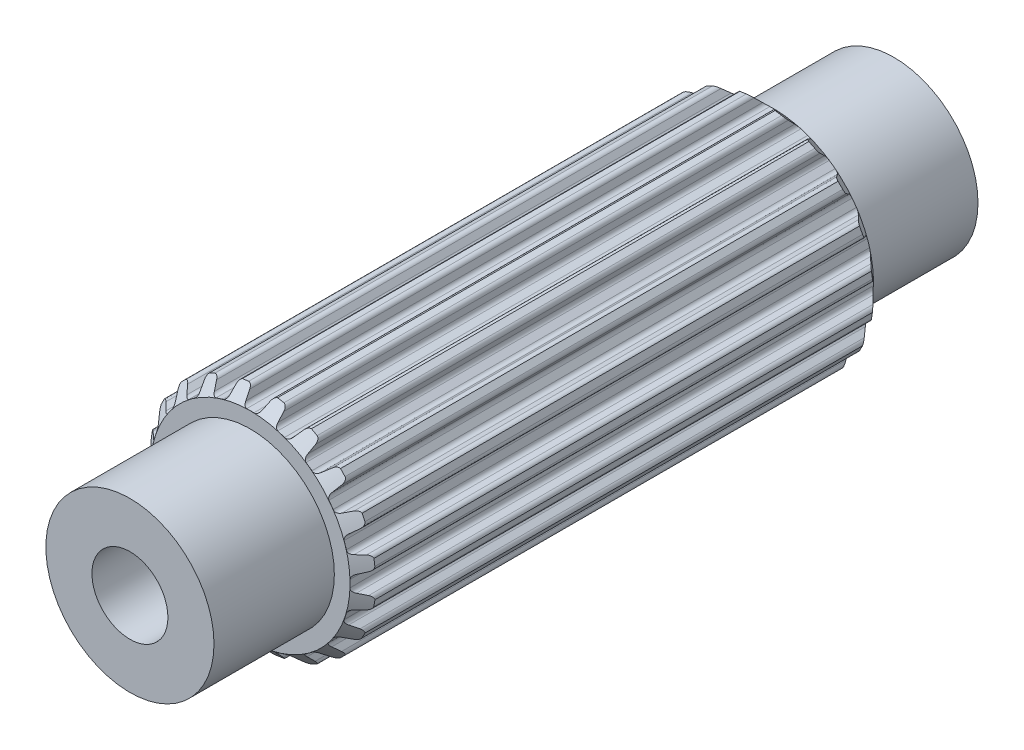
SolidWorks part; units mm, degrees
ref_plane "Front Plane" through (0, 0, 0) normal (0, 0, 1) x (1, 0, 0)
ref_plane "Top Plane" through (0, 0, 0) normal (0, 1, 0) x (1, 0, 0)
ref_plane "Right Plane" through (0, 0, 0) normal (1, 0, 0) x (0, 0, -1)
sketch "Sketch1" plane through (0, 0, 0) normal (0, 0, 1) x (1, 0, 0)
  line L0 (-0.1069, 2.9699) -> (0.1069, 2.9699)
  line L1 (0.3159, 3.2375) -> (0.2537, 3.0575)
  line L2 (-0.2964, 3.2367) -> (-0.2318, 3.0575)
  line L3 (-0.2964, 3.2367) -> (0.3159, 3.2375) construction
  line L4 (0, 3.3252) -> (0, 0) construction
  line L5 (-0.2318, 3.0575) -> (0.2537, 3.0575) construction
  line L6 (-0.4281, 3.3241) -> (0.4281, 3.3263) construction
  line L7 (0.7183, 3.1698) -> (0.7244, 2.9795)
  line L8 (0.816, 2.8576) -> (1.0195, 2.7915)
  line L9 (1.3009, 2.9815) -> (1.1862, 2.8295)
  line L10 (1.6627, 2.7927) -> (1.6097, 2.6099)
  line L11 (1.6591, 2.4655) -> (1.8322, 2.3398)
  line L12 (2.1585, 2.4335) -> (2.0025, 2.3245)
  line L13 (2.4443, 2.1423) -> (2.3374, 1.9847)
  line L14 (2.3398, 1.8322) -> (2.4655, 1.6591)
  line L15 (2.8049, 1.6474) -> (2.6228, 1.5919)
  line L16 (2.9866, 1.2821) -> (2.8363, 1.1653)
  line L17 (2.7915, 1.0195) -> (2.8576, 0.816)
  line L18 (3.1767, 0.7) -> (2.9863, 0.7035)
  line L19 (3.2367, 0.2964) -> (3.0575, 0.2318)
  line L20 (2.9699, 0.1069) -> (2.9699, -0.1069)
  line L21 (3.2375, -0.3159) -> (3.0575, -0.2537)
  line L22 (3.1698, -0.7183) -> (2.9795, -0.7244)
  line L23 (2.8576, -0.816) -> (2.7915, -1.0195)
  line L24 (2.9815, -1.3009) -> (2.8295, -1.1862)
  line L25 (2.7927, -1.6627) -> (2.6099, -1.6097)
  line L26 (2.4655, -1.6591) -> (2.3398, -1.8322)
  line L27 (2.4335, -2.1585) -> (2.3245, -2.0025)
  line L28 (2.1423, -2.4443) -> (1.9847, -2.3374)
  line L29 (1.8322, -2.3398) -> (1.6591, -2.4655)
  line L30 (1.6474, -2.8049) -> (1.5919, -2.6228)
  line L31 (1.2821, -2.9866) -> (1.1653, -2.8363)
  line L32 (1.0195, -2.7915) -> (0.816, -2.8576)
  line L33 (0.7, -3.1767) -> (0.7035, -2.9863)
  line L34 (0.2964, -3.2367) -> (0.2318, -3.0575)
  line L35 (0.1069, -2.9699) -> (-0.1069, -2.9699)
  line L36 (-0.3159, -3.2375) -> (-0.2537, -3.0575)
  line L37 (-0.7183, -3.1698) -> (-0.7244, -2.9795)
  line L38 (-0.816, -2.8576) -> (-1.0195, -2.7915)
  line L39 (-1.3009, -2.9815) -> (-1.1862, -2.8295)
  line L40 (-1.6627, -2.7927) -> (-1.6097, -2.6099)
  line L41 (-1.6591, -2.4655) -> (-1.8322, -2.3398)
  line L42 (-2.1585, -2.4335) -> (-2.0025, -2.3245)
  line L43 (-2.4443, -2.1423) -> (-2.3374, -1.9847)
  line L44 (-2.3398, -1.8322) -> (-2.4655, -1.6591)
  line L45 (-2.8049, -1.6474) -> (-2.6228, -1.5919)
  line L46 (-2.9866, -1.2821) -> (-2.8363, -1.1653)
  line L47 (-2.7915, -1.0195) -> (-2.8576, -0.816)
  line L48 (-3.1767, -0.7) -> (-2.9863, -0.7035)
  line L49 (-3.2367, -0.2964) -> (-3.0575, -0.2318)
  line L50 (-2.9699, -0.1069) -> (-2.9699, 0.1069)
  line L51 (-3.2375, 0.3159) -> (-3.0575, 0.2537)
  line L52 (-3.1698, 0.7183) -> (-2.9795, 0.7244)
  line L53 (-2.8576, 0.816) -> (-2.7915, 1.0195)
  line L54 (-2.9815, 1.3009) -> (-2.8295, 1.1862)
  line L55 (-2.7927, 1.6627) -> (-2.6099, 1.6097)
  line L56 (-2.4655, 1.6591) -> (-2.3398, 1.8322)
  line L57 (-2.4335, 2.1585) -> (-2.3245, 2.0025)
  line L58 (-2.1423, 2.4443) -> (-1.9847, 2.3374)
  line L59 (-1.8322, 2.3398) -> (-1.6591, 2.4655)
  line L60 (-1.6474, 2.8049) -> (-1.5919, 2.6228)
  line L61 (-1.2821, 2.9866) -> (-1.1653, 2.8363)
  line L62 (-1.0195, 2.7915) -> (-0.816, 2.8576)
  line L63 (-0.7, 3.1767) -> (-0.7035, 2.9863)
  line L64 (0.4281, 3.3263) -> (0.62, 3.2938)
  line L65 (1.4351, 3.0312) -> (1.6075, 2.9409)
  line L66 (2.3015, 2.4394) -> (2.4376, 2.3003)
  line L67 (2.9427, 1.6088) -> (3.0291, 1.4344)
  line L68 (3.2958, 0.6207) -> (3.3241, 0.4281)
  line L69 (3.3263, -0.4281) -> (3.2938, -0.62)
  line L70 (3.0312, -1.4351) -> (2.9409, -1.6075)
  line L71 (2.4394, -2.3015) -> (2.3003, -2.4376)
  line L72 (1.6088, -2.9427) -> (1.4344, -3.0291)
  line L73 (0.6207, -3.2958) -> (0.4281, -3.3241)
  line L74 (-0.4281, -3.3263) -> (-0.62, -3.2938)
  line L75 (-1.4351, -3.0312) -> (-1.6075, -2.9409)
  line L76 (-2.3015, -2.4394) -> (-2.4376, -2.3003)
  line L77 (-2.9427, -1.6088) -> (-3.0291, -1.4344)
  line L78 (-3.2958, -0.6207) -> (-3.3241, -0.4281)
  line L79 (-3.3263, 0.4281) -> (-3.2938, 0.62)
  line L80 (-3.0312, 1.4351) -> (-2.9409, 1.6075)
  line L81 (-2.4394, 2.3015) -> (-2.3003, 2.4376)
  line L82 (-1.6088, 2.9427) -> (-1.4344, 3.0291)
  line L83 (-0.6207, 3.2958) -> (-0.4281, 3.3241)
  arc A0 (0.2537, 3.0575) -> (0.1069, 2.9699) centre (0.1283, 3.1009) cw
  arc A1 (-0.2318, 3.0575) -> (-0.1069, 2.9699) centre (-0.1069, 3.1026) ccw
  arc A2 (0.62, 3.2938) -> (0.7183, 3.1698) centre (0.5856, 3.1656) cw
  arc A3 (0.7244, 2.9795) -> (0.816, 2.8576) centre (0.857, 2.9838) ccw
  arc A4 (-0.4281, 3.3241) -> (-0.2964, 3.2367) centre (-0.4213, 3.1916) cw
  arc A5 (0.4281, 3.3263) -> (0.3159, 3.2375) centre (0.4413, 3.1942) ccw
  arc A6 (1.1862, 2.8295) -> (1.0195, 2.7915) centre (1.0802, 2.9095) cw
  arc A7 (1.4351, 3.0312) -> (1.3009, 2.9815) centre (1.4068, 2.9015) ccw
  arc A8 (1.6075, 2.9409) -> (1.6627, 2.7927) centre (1.5352, 2.8297) cw
  arc A9 (1.6097, 2.6099) -> (1.6591, 2.4655) centre (1.7371, 2.5729) ccw
  arc A10 (2.0025, 2.3245) -> (1.8322, 2.3398) centre (1.9264, 2.4332) cw
  arc A11 (2.3015, 2.4394) -> (2.1585, 2.4335) centre (2.2346, 2.3248) ccw
  arc A12 (2.4376, 2.3003) -> (2.4443, 2.1423) centre (2.3345, 2.2168) cw
  arc A13 (2.3374, 1.9847) -> (2.3398, 1.8322) centre (2.4472, 1.9102) ccw
  arc A14 (2.6228, 1.5919) -> (2.4655, 1.6591) centre (2.5841, 1.7189) cw
  arc A15 (2.9427, 1.6088) -> (2.8049, 1.6474) centre (2.8436, 1.5205) ccw
  arc A16 (3.0291, 1.4344) -> (2.9866, 1.2821) centre (2.9052, 1.3869) cw
  arc A17 (2.8363, 1.1653) -> (2.7915, 1.0195) centre (2.9177, 1.0605) ccw
  arc A18 (2.9863, 0.7035) -> (2.8576, 0.816) centre (2.9887, 0.8362) cw
  arc A19 (3.2958, 0.6207) -> (3.1767, 0.7) centre (3.1743, 0.5673) ccw
  arc A20 (3.3241, 0.4281) -> (3.2367, 0.2964) centre (3.1916, 0.4213) cw
  arc A21 (3.0575, 0.2318) -> (2.9699, 0.1069) centre (3.1026, 0.1069) ccw
  arc A22 (3.0575, -0.2537) -> (2.9699, -0.1069) centre (3.1009, -0.1283) cw
  arc A23 (3.3263, -0.4281) -> (3.2375, -0.3159) centre (3.1942, -0.4413) ccw
  arc A24 (3.2938, -0.62) -> (3.1698, -0.7183) centre (3.1656, -0.5856) cw
  arc A25 (2.9795, -0.7244) -> (2.8576, -0.816) centre (2.9838, -0.857) ccw
  arc A26 (2.8295, -1.1862) -> (2.7915, -1.0195) centre (2.9095, -1.0802) cw
  arc A27 (3.0312, -1.4351) -> (2.9815, -1.3009) centre (2.9015, -1.4068) ccw
  arc A28 (2.9409, -1.6075) -> (2.7927, -1.6627) centre (2.8297, -1.5352) cw
  arc A29 (2.6099, -1.6097) -> (2.4655, -1.6591) centre (2.5729, -1.7371) ccw
  arc A30 (2.3245, -2.0025) -> (2.3398, -1.8322) centre (2.4332, -1.9264) cw
  arc A31 (2.4394, -2.3015) -> (2.4335, -2.1585) centre (2.3248, -2.2346) ccw
  arc A32 (2.3003, -2.4376) -> (2.1423, -2.4443) centre (2.2168, -2.3345) cw
  arc A33 (1.9847, -2.3374) -> (1.8322, -2.3398) centre (1.9102, -2.4472) ccw
  arc A34 (1.5919, -2.6228) -> (1.6591, -2.4655) centre (1.7189, -2.5841) cw
  arc A35 (1.6088, -2.9427) -> (1.6474, -2.8049) centre (1.5205, -2.8436) ccw
  arc A36 (1.4344, -3.0291) -> (1.2821, -2.9866) centre (1.3869, -2.9052) cw
  arc A37 (1.1653, -2.8363) -> (1.0195, -2.7915) centre (1.0605, -2.9177) ccw
  arc A38 (0.7035, -2.9863) -> (0.816, -2.8576) centre (0.8362, -2.9887) cw
  arc A39 (0.6207, -3.2958) -> (0.7, -3.1767) centre (0.5673, -3.1743) ccw
  arc A40 (0.4281, -3.3241) -> (0.2964, -3.2367) centre (0.4213, -3.1916) cw
  arc A41 (0.2318, -3.0575) -> (0.1069, -2.9699) centre (0.1069, -3.1026) ccw
  arc A42 (-0.2537, -3.0575) -> (-0.1069, -2.9699) centre (-0.1283, -3.1009) cw
  arc A43 (-0.4281, -3.3263) -> (-0.3159, -3.2375) centre (-0.4413, -3.1942) ccw
  arc A44 (-0.62, -3.2938) -> (-0.7183, -3.1698) centre (-0.5856, -3.1656) cw
  arc A45 (-0.7244, -2.9795) -> (-0.816, -2.8576) centre (-0.857, -2.9838) ccw
  arc A46 (-1.1862, -2.8295) -> (-1.0195, -2.7915) centre (-1.0802, -2.9095) cw
  arc A47 (-1.4351, -3.0312) -> (-1.3009, -2.9815) centre (-1.4068, -2.9015) ccw
  arc A48 (-1.6075, -2.9409) -> (-1.6627, -2.7927) centre (-1.5352, -2.8297) cw
  arc A49 (-1.6097, -2.6099) -> (-1.6591, -2.4655) centre (-1.7371, -2.5729) ccw
  arc A50 (-2.0025, -2.3245) -> (-1.8322, -2.3398) centre (-1.9264, -2.4332) cw
  arc A51 (-2.3015, -2.4394) -> (-2.1585, -2.4335) centre (-2.2346, -2.3248) ccw
  arc A52 (-2.4376, -2.3003) -> (-2.4443, -2.1423) centre (-2.3345, -2.2168) cw
  arc A53 (-2.3374, -1.9847) -> (-2.3398, -1.8322) centre (-2.4472, -1.9102) ccw
  arc A54 (-2.6228, -1.5919) -> (-2.4655, -1.6591) centre (-2.5841, -1.7189) cw
  arc A55 (-2.9427, -1.6088) -> (-2.8049, -1.6474) centre (-2.8436, -1.5205) ccw
  arc A56 (-3.0291, -1.4344) -> (-2.9866, -1.2821) centre (-2.9052, -1.3869) cw
  arc A57 (-2.8363, -1.1653) -> (-2.7915, -1.0195) centre (-2.9177, -1.0605) ccw
  arc A58 (-2.9863, -0.7035) -> (-2.8576, -0.816) centre (-2.9887, -0.8362) cw
  arc A59 (-3.2958, -0.6207) -> (-3.1767, -0.7) centre (-3.1743, -0.5673) ccw
  arc A60 (-3.3241, -0.4281) -> (-3.2367, -0.2964) centre (-3.1916, -0.4213) cw
  arc A61 (-3.0575, -0.2318) -> (-2.9699, -0.1069) centre (-3.1026, -0.1069) ccw
  arc A62 (-3.0575, 0.2537) -> (-2.9699, 0.1069) centre (-3.1009, 0.1283) cw
  arc A63 (-3.3263, 0.4281) -> (-3.2375, 0.3159) centre (-3.1942, 0.4413) ccw
  arc A64 (-3.2938, 0.62) -> (-3.1698, 0.7183) centre (-3.1656, 0.5856) cw
  arc A65 (-2.9795, 0.7244) -> (-2.8576, 0.816) centre (-2.9838, 0.857) ccw
  arc A66 (-2.8295, 1.1862) -> (-2.7915, 1.0195) centre (-2.9095, 1.0802) cw
  arc A67 (-3.0312, 1.4351) -> (-2.9815, 1.3009) centre (-2.9015, 1.4068) ccw
  arc A68 (-2.9409, 1.6075) -> (-2.7927, 1.6627) centre (-2.8297, 1.5352) cw
  arc A69 (-2.6099, 1.6097) -> (-2.4655, 1.6591) centre (-2.5729, 1.7371) ccw
  arc A70 (-2.3245, 2.0025) -> (-2.3398, 1.8322) centre (-2.4332, 1.9264) cw
  arc A71 (-2.4394, 2.3015) -> (-2.4335, 2.1585) centre (-2.3248, 2.2346) ccw
  arc A72 (-2.3003, 2.4376) -> (-2.1423, 2.4443) centre (-2.2168, 2.3345) cw
  arc A73 (-1.9847, 2.3374) -> (-1.8322, 2.3398) centre (-1.9102, 2.4472) ccw
  arc A74 (-1.5919, 2.6228) -> (-1.6591, 2.4655) centre (-1.7189, 2.5841) cw
  arc A75 (-1.6088, 2.9427) -> (-1.6474, 2.8049) centre (-1.5205, 2.8436) ccw
  arc A76 (-1.4344, 3.0291) -> (-1.2821, 2.9866) centre (-1.3869, 2.9052) cw
  arc A77 (-1.1653, 2.8363) -> (-1.0195, 2.7915) centre (-1.0605, 2.9177) ccw
  arc A78 (-0.7035, 2.9863) -> (-0.816, 2.8576) centre (-0.8362, 2.9887) cw
  arc A79 (-0.6207, 3.2958) -> (-0.7, 3.1767) centre (-0.5673, 3.1743) ccw
  point P14 (0, 2.9699)
  point P247 (0, 0)
  dimension "D4" = 0.1327
  dimension "D8" = 20
  dimension "D1" = 2.9699
  dimension "D2" = 0.2139
  dimension "D3" = 0.1904
  dimension "D5" = 0.0877
  dimension "D6" = 0.4855
  dimension "D7" = 0.8563
extrude "Boss-Extrude1" add sketch "Sketch1" along normal mid plane 15.5702
sketch "Sketch2" plane through (0, 0, 0) normal (0, 0, 1) x (1, 0, 0)
  circle A0 centre (0, 0) radius 2.5019
  dimension "D1" = 5.0038
extrude "Boss-Extrude2" add sketch "Sketch2" along normal mid plane 22.733
sketch "Sketch4" plane through (0, 0, 11.3665) normal (0, 0, 1) x (1, 0, 0)
  circle A0 centre (0, 0) radius 2.5019 construction
  point P0 (0, 0)
sketch "Sketch5" plane through (0, 0, -11.3665) normal (0, 0, -1) x (-1, 0, 0)
  circle A0 centre (0, 0) radius 2.5019 construction
  point P0 (0, 0)
sketch "Sketch3" plane through (0, 0, 0) normal (1, 0, 0) x (0, 0, -1)
  line L0 (-6.6539, 4.1011) -> (-7.7851, 2.9699)
  line L1 (-7.7851, 2.9699) -> (-7.7851, 4.1011)
  line L2 (-7.7851, 4.1011) -> (-6.6539, 4.1011)
  line L3 (-7.7851, 2.5019) -> (-7.7851, -2.5019) construction
  line L5 (-14.3608, 0) -> (13.2171, 0) construction
  line L7 (7.7851, 4.499) -> (7.7851, 2.9699)
  line L8 (7.7851, 2.9699) -> (7.0206, 3.7344)
  line L9 (7.0206, 3.7344) -> (7.7851, 4.499)
  line L10 (7.7851, -2.5019) -> (7.7851, 2.5019) construction
  point P6 (-4.866, 6.1438)
  dimension "D1" = 45
  dimension "D2" = 45
revolve "Cut-Revolve1" cut sketch "Sketch3" angle 360 about L5
sketch "Sketch6" plane through (0, 0, 0) normal (0, 0, 1) x (1, 0, 0)
  circle A0 centre (0, 0) radius 1.1303
  dimension "D1" = 2.2606
extrude "Cut-Extrude1" cut sketch "Sketch6" against normal up to surface and the other way up to surface up to face at (2.5019, 0, -11.3665) other way up to face at (2.5019, 0, 11.3665)
sketch "Sketch7" plane through (0, 0, 0) normal (0, 0, 1) x (1, 0, 0)
  circle A0 centre (0, 0) radius 1.1303
  circle A1 centre (0, 0) radius 1.1303 construction
extrude "Boss-Extrude3" add sketch "Sketch7" along normal offset from surface 9.525 and the other way offset from surface (1.8415 mm away) 9.525 up to face at (1.1303, 0, 11.3665) other way up to face at (1.1303, 0, -11.3665)
